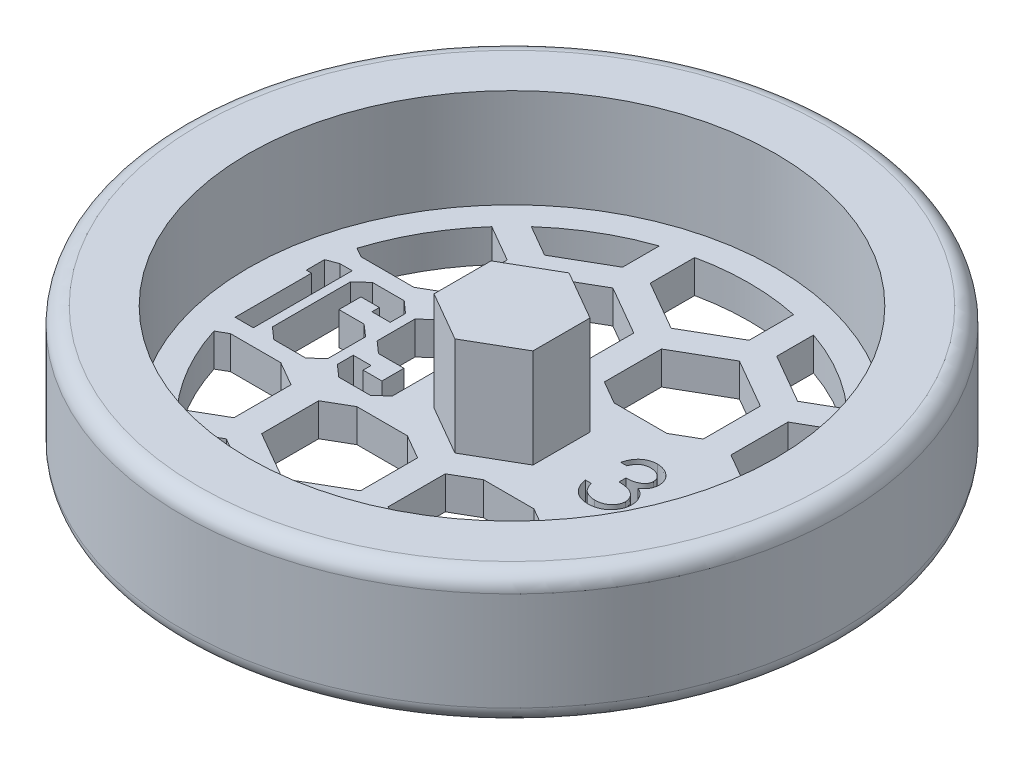
SolidWorks part; units mm, degrees
ref_plane "Front Plane" through (0, 0, 0) normal (0, 0, 1) x (1, 0, 0)
ref_plane "Top Plane" through (0, 0, 0) normal (0, 1, 0) x (1, 0, 0)
ref_plane "Right Plane" through (0, 0, 0) normal (1, 0, 0) x (0, 0, -1)
sketch "Sketch1" plane through (0, 0, 0) normal (0, 0, 1) x (1, 0, 0)
  line L0 (0, 0) -> (30.1625, 0)
  line L1 (31.75, 1.5875) -> (31.75, 11.1125)
  line L2 (30.1625, 12.7) -> (25.4, 12.7)
  line L3 (25.4, 12.7) -> (25.4, 3.175)
  line L4 (25.4, 3.175) -> (0, 3.175)
  line L5 (0, 3.175) -> (0, 0)
  arc A0 (30.1625, 0) -> (31.75, 1.5875) centre (30.1625, 1.5875) ccw
  arc A1 (31.75, 11.1125) -> (30.1625, 12.7) centre (30.1625, 11.1125) ccw
  dimension "D5" = 1.5875
  dimension "D1" = 6.35
  dimension "D2" = 3.175
  dimension "D3" = 25.4
  dimension "D4" = 9.525
revolve "Revolve1" add sketch "Sketch1" angle 360 about L5
sketch "Sketch2" plane through (0, 3.175, 0) normal (0, 1, 0) x (1, 0, 0)
  line L1 (0, -5.4993) -> (4.7625, -2.7496)
  line L2 (4.7625, -2.7496) -> (4.7625, 2.7496)
  line L3 (4.7625, 2.7496) -> (0, 5.4993)
  line L4 (0, 5.4993) -> (-4.7625, 2.7496)
  line L5 (-4.7625, 2.7496) -> (-4.7625, -2.7496)
  line L6 (-4.7625, -2.7496) -> (0, -5.4993)
  circle A0 centre (0, 0) radius 4.7625 construction
  dimension "D1" = 9.525
extrude "Boss-Extrude1" add sketch "Sketch2" along normal blind 9.525
sketch "Sketch3" plane through (0, 3.175, 0) normal (0, 1, 0) x (1, 0, 0)
  line L0 (-4.7625, 0) -> (-25.4, 0) construction
  line L1 (-4.7625, 2.7496) -> (-4.7625, -2.7496) construction
  line L2 (-25.4, -4.7625) -> (-4.7625, -4.7625) construction
  line L3 (4.7625, 0) -> (25.4, 0) construction
  line L4 (4.7625, -2.7496) -> (4.7625, 2.7496) construction
  line L5 (4.7625, -3.175) -> (25.4, -3.175) construction
  circle A0 centre (0, 0) radius 25.4 construction
  circle A1 centre (0, 0) radius 25.4 construction
  text T0 "169" font "Jersey M54" height 9.525
  text T1 "3/8" font "Century Gothic" height 6.35
  dimension "D1" = 4.7625
  dimension "D2" = 3.175
extrude "Cut-Extrude1" cut sketch "Sketch3" against normal through all both and the other way through all
sketch "Sketch4" plane through (0, 3.175, 0) normal (0, 1, 0) x (1, 0, 0)
  line L0 (0, -6.35) -> (0, 6.35)
  line L1 (-21.9604, 6.35) -> (21.9604, 6.35)
  line L2 (-21.9604, -6.35) -> (21.9604, -6.35)
  line L3 (7.4295, -2.7496) -> (12.192, -5.4993)
  line L4 (0, -5.4993) -> (4.7625, -2.7496)
  line L5 (4.7625, -2.7496) -> (4.7625, 2.7496)
  line L6 (4.7625, 2.7496) -> (0, 5.4993)
  line L7 (0, 5.4993) -> (-4.7625, 2.7496)
  line L8 (-4.7625, 2.7496) -> (-4.7625, -2.7496)
  line L9 (-4.7625, -2.7496) -> (0, -5.4993)
  line L10 (6.0325, -4.9493) -> (1.27, -7.699)
  line L11 (1.27, -7.699) -> (1.27, -13.1982)
  line L12 (1.27, -13.1982) -> (6.0325, -15.9479)
  line L13 (6.0325, -15.9479) -> (10.795, -13.1982)
  line L14 (10.795, -13.1982) -> (10.795, -7.699)
  line L15 (10.795, -7.699) -> (6.0325, -4.9493)
  line L16 (7.4295, 2.7496) -> (7.4295, -2.7496)
  line L17 (12.192, 5.4993) -> (7.4295, 2.7496)
  line L18 (16.9545, 2.7496) -> (12.192, 5.4993)
  line L19 (16.9545, -2.7496) -> (16.9545, 2.7496)
  line L20 (12.192, -5.4993) -> (16.9545, -2.7496)
  line L21 (18.2245, -4.9493) -> (13.462, -7.699)
  line L22 (13.462, -7.699) -> (13.462, -13.1982)
  line L23 (13.462, -13.1982) -> (18.2245, -15.9479)
  line L24 (18.2245, -15.9479) -> (22.987, -13.1982)
  line L25 (22.987, -13.1982) -> (22.987, -7.699)
  line L26 (22.987, -7.699) -> (18.2245, -4.9493)
  line L27 (19.6215, -2.7496) -> (24.384, -5.4993)
  line L28 (19.6215, 2.7496) -> (19.6215, -2.7496)
  line L29 (24.384, 5.4993) -> (19.6215, 2.7496)
  line L30 (29.1465, 2.7496) -> (24.384, 5.4993)
  line L31 (29.1465, -2.7496) -> (29.1465, 2.7496)
  line L32 (24.384, -5.4993) -> (29.1465, -2.7496)
  line L33 (30.4165, -4.9493) -> (25.654, -7.699)
  line L34 (25.654, -7.699) -> (25.654, -13.1982)
  line L35 (25.654, -13.1982) -> (30.4165, -15.9479)
  line L36 (30.4165, -15.9479) -> (35.179, -13.1982)
  line L37 (35.179, -13.1982) -> (35.179, -7.699)
  line L38 (35.179, -7.699) -> (30.4165, -4.9493)
  line L39 (-16.9545, -2.7496) -> (-12.192, -5.4993)
  line L40 (-16.9545, 2.7496) -> (-16.9545, -2.7496)
  line L41 (-12.192, 5.4993) -> (-16.9545, 2.7496)
  line L42 (-7.4295, 2.7496) -> (-12.192, 5.4993)
  line L43 (-7.4295, -2.7496) -> (-7.4295, 2.7496)
  line L44 (-12.192, -5.4993) -> (-7.4295, -2.7496)
  line L45 (-6.1595, -4.9493) -> (-10.922, -7.699)
  line L46 (-10.922, -7.699) -> (-10.922, -13.1982)
  line L47 (-10.922, -13.1982) -> (-6.1595, -15.9479)
  line L48 (-6.1595, -15.9479) -> (-1.397, -13.1982)
  line L49 (-1.397, -13.1982) -> (-1.397, -7.699)
  line L50 (-1.397, -7.699) -> (-6.1595, -4.9493)
  line L51 (-29.1465, -2.7496) -> (-24.384, -5.4993)
  line L52 (-29.1465, 2.7496) -> (-29.1465, -2.7496)
  line L53 (-24.384, 5.4993) -> (-29.1465, 2.7496)
  line L54 (-19.6215, 2.7496) -> (-24.384, 5.4993)
  line L55 (-19.6215, -2.7496) -> (-19.6215, 2.7496)
  line L56 (-24.384, -5.4993) -> (-19.6215, -2.7496)
  line L57 (-18.3515, -4.9493) -> (-23.114, -7.699)
  line L58 (-23.114, -7.699) -> (-23.114, -13.1982)
  line L59 (-23.114, -13.1982) -> (-18.3515, -15.9479)
  line L60 (-18.3515, -15.9479) -> (-13.589, -13.1982)
  line L61 (-13.589, -13.1982) -> (-13.589, -7.699)
  line L62 (-13.589, -7.699) -> (-18.3515, -4.9493)
  line L63 (-29.1465, 18.0784) -> (-24.384, 15.3287)
  line L64 (-24.384, 15.3287) -> (-19.6215, 18.0784)
  line L65 (-19.6215, 18.0784) -> (-19.6215, 23.5776)
  line L66 (-19.6215, 23.5776) -> (-24.384, 26.3273)
  line L67 (-24.384, 26.3273) -> (-29.1465, 23.5776)
  line L68 (-29.1465, 23.5776) -> (-29.1465, 18.0784)
  line L69 (-18.3515, 15.8787) -> (-23.114, 13.129)
  line L70 (-23.114, 13.129) -> (-23.114, 7.6298)
  line L71 (-23.114, 7.6298) -> (-18.3515, 4.8801)
  line L72 (-18.3515, 4.8801) -> (-13.589, 7.6298)
  line L73 (-13.589, 7.6298) -> (-13.589, 13.129)
  line L74 (-13.589, 13.129) -> (-18.3515, 15.8787)
  line L75 (-16.9545, 18.0784) -> (-12.192, 15.3287)
  line L76 (-12.192, 15.3287) -> (-7.4295, 18.0784)
  line L77 (-7.4295, 18.0784) -> (-7.4295, 23.5776)
  line L78 (-7.4295, 23.5776) -> (-12.192, 26.3273)
  line L79 (-12.192, 26.3273) -> (-16.9545, 23.5776)
  line L80 (-16.9545, 23.5776) -> (-16.9545, 18.0784)
  line L81 (-6.1595, 15.8787) -> (-10.922, 13.129)
  line L82 (-10.922, 13.129) -> (-10.922, 7.6298)
  line L83 (-10.922, 7.6298) -> (-6.1595, 4.8801)
  line L84 (-6.1595, 4.8801) -> (-1.397, 7.6298)
  line L85 (-1.397, 7.6298) -> (-1.397, 13.129)
  line L86 (-1.397, 13.129) -> (-6.1595, 15.8787)
  line L87 (6.0325, 15.8787) -> (1.27, 13.129)
  line L88 (1.27, 13.129) -> (1.27, 7.6298)
  line L89 (1.27, 7.6298) -> (6.0325, 4.8801)
  line L90 (6.0325, 4.8801) -> (10.795, 7.6298)
  line L91 (10.795, 7.6298) -> (10.795, 13.129)
  line L92 (10.795, 13.129) -> (6.0325, 15.8787)
  line L93 (-4.7625, 18.0784) -> (0, 15.3287)
  line L94 (-4.7625, 23.5776) -> (-4.7625, 18.0784)
  line L95 (0, 26.3273) -> (-4.7625, 23.5776)
  line L96 (4.7625, 23.5776) -> (0, 26.3273)
  line L97 (4.7625, 18.0784) -> (4.7625, 23.5776)
  line L98 (0, 15.3287) -> (4.7625, 18.0784)
  line L99 (7.4295, 18.0784) -> (12.192, 15.3287)
  line L100 (12.192, 15.3287) -> (16.9545, 18.0784)
  line L101 (16.9545, 18.0784) -> (16.9545, 23.5776)
  line L102 (16.9545, 23.5776) -> (12.192, 26.3273)
  line L103 (12.192, 26.3273) -> (7.4295, 23.5776)
  line L104 (7.4295, 23.5776) -> (7.4295, 18.0784)
  line L105 (19.6215, 18.0784) -> (24.384, 15.3287)
  line L106 (24.384, 15.3287) -> (29.1465, 18.0784)
  line L107 (29.1465, 18.0784) -> (29.1465, 23.5776)
  line L108 (29.1465, 23.5776) -> (24.384, 26.3273)
  line L109 (24.384, 26.3273) -> (19.6215, 23.5776)
  line L110 (19.6215, 23.5776) -> (19.6215, 18.0784)
  line L111 (18.2245, 15.8787) -> (13.462, 13.129)
  line L112 (13.462, 13.129) -> (13.462, 7.6298)
  line L113 (13.462, 7.6298) -> (18.2245, 4.8801)
  line L114 (18.2245, 4.8801) -> (22.987, 7.6298)
  line L115 (22.987, 7.6298) -> (22.987, 13.129)
  line L116 (22.987, 13.129) -> (18.2245, 15.8787)
  line L117 (30.4165, 15.8787) -> (25.654, 13.129)
  line L118 (25.654, 13.129) -> (25.654, 7.6298)
  line L119 (25.654, 7.6298) -> (30.4165, 4.8801)
  line L120 (30.4165, 4.8801) -> (35.179, 7.6298)
  line L121 (35.179, 7.6298) -> (35.179, 13.129)
  line L122 (35.179, 13.129) -> (30.4165, 15.8787)
  line L123 (-29.1465, -23.5776) -> (-24.384, -26.3273)
  line L124 (-24.384, -26.3273) -> (-19.6215, -23.5776)
  line L125 (-19.6215, -23.5776) -> (-19.6215, -18.0784)
  line L126 (-19.6215, -18.0784) -> (-24.384, -15.3287)
  line L127 (-24.384, -15.3287) -> (-29.1465, -18.0784)
  line L128 (-29.1465, -18.0784) -> (-29.1465, -23.5776)
  line L129 (-18.3515, -25.7773) -> (-23.114, -28.527)
  line L130 (-23.114, -28.527) -> (-23.114, -34.0262)
  line L131 (-23.114, -34.0262) -> (-18.3515, -36.7759)
  line L132 (-18.3515, -36.7759) -> (-13.589, -34.0262)
  line L133 (-13.589, -34.0262) -> (-13.589, -28.527)
  line L134 (-13.589, -28.527) -> (-18.3515, -25.7773)
  line L135 (-16.9545, -23.5776) -> (-12.192, -26.3273)
  line L136 (-12.192, -26.3273) -> (-7.4295, -23.5776)
  line L137 (-7.4295, -23.5776) -> (-7.4295, -18.0784)
  line L138 (-7.4295, -18.0784) -> (-12.192, -15.3287)
  line L139 (-12.192, -15.3287) -> (-16.9545, -18.0784)
  line L140 (-16.9545, -18.0784) -> (-16.9545, -23.5776)
  line L141 (-6.1595, -25.7773) -> (-10.922, -28.527)
  line L142 (-10.922, -28.527) -> (-10.922, -34.0262)
  line L143 (-10.922, -34.0262) -> (-6.1595, -36.7759)
  line L144 (-6.1595, -36.7759) -> (-1.397, -34.0262)
  line L145 (-1.397, -34.0262) -> (-1.397, -28.527)
  line L146 (-1.397, -28.527) -> (-6.1595, -25.7773)
  line L147 (6.0325, -25.7773) -> (1.27, -28.527)
  line L148 (1.27, -28.527) -> (1.27, -34.0262)
  line L149 (1.27, -34.0262) -> (6.0325, -36.7759)
  line L150 (6.0325, -36.7759) -> (10.795, -34.0262)
  line L151 (10.795, -34.0262) -> (10.795, -28.527)
  line L152 (10.795, -28.527) -> (6.0325, -25.7773)
  line L153 (-4.7625, -23.5776) -> (0, -26.3273)
  line L154 (-4.7625, -18.0784) -> (-4.7625, -23.5776)
  line L155 (0, -15.3287) -> (-4.7625, -18.0784)
  line L156 (4.7625, -18.0784) -> (0, -15.3287)
  line L157 (4.7625, -23.5776) -> (4.7625, -18.0784)
  line L158 (0, -26.3273) -> (4.7625, -23.5776)
  line L159 (7.4295, -23.5776) -> (12.192, -26.3273)
  line L160 (12.192, -26.3273) -> (16.9545, -23.5776)
  line L161 (16.9545, -23.5776) -> (16.9545, -18.0784)
  line L162 (16.9545, -18.0784) -> (12.192, -15.3287)
  line L163 (12.192, -15.3287) -> (7.4295, -18.0784)
  line L164 (7.4295, -18.0784) -> (7.4295, -23.5776)
  line L165 (19.6215, -23.5776) -> (24.384, -26.3273)
  line L166 (24.384, -26.3273) -> (29.1465, -23.5776)
  line L167 (29.1465, -23.5776) -> (29.1465, -18.0784)
  line L168 (29.1465, -18.0784) -> (24.384, -15.3287)
  line L169 (24.384, -15.3287) -> (19.6215, -18.0784)
  line L170 (19.6215, -18.0784) -> (19.6215, -23.5776)
  line L171 (18.2245, -25.7773) -> (13.462, -28.527)
  line L172 (13.462, -28.527) -> (13.462, -34.0262)
  line L173 (13.462, -34.0262) -> (18.2245, -36.7759)
  line L174 (18.2245, -36.7759) -> (22.987, -34.0262)
  line L175 (22.987, -34.0262) -> (22.987, -28.527)
  line L176 (22.987, -28.527) -> (18.2245, -25.7773)
  line L177 (30.4165, -25.7773) -> (25.654, -28.527)
  line L178 (25.654, -28.527) -> (25.654, -34.0262)
  line L179 (25.654, -34.0262) -> (30.4165, -36.7759)
  line L180 (30.4165, -36.7759) -> (35.179, -34.0262)
  line L181 (35.179, -34.0262) -> (35.179, -28.527)
  line L182 (35.179, -28.527) -> (30.4165, -25.7773)
  circle A0 centre (0, 0) radius 22.86
  circle A1 centre (0, 0) radius 4.7625 construction
  circle A2 centre (6.0325, -10.4486) radius 4.7625 construction
  point P6 (0, 0)
  point P9 (0, 6.35)
  point P12 (0, -6.35)
  dimension "D1" = 45.72
  dimension "D2" = 12.7
  dimension "D3" = 9.525
  dimension "D4" = 9.525
  dimension "D5" = 2.54
  dimension "D6" = 1.27
  dimension "D9" = 2.1997
  dimension "D7" = 3
  dimension "D8" = 3
  dimension "D10" = 2
  dimension "D11" = 2
extrude "Cut-Extrude3" cut sketch "Sketch4" against normal through all both and the other way through all contours L74 A0 L71 L1 L72 L73 | L77 A0 L75 L76 | L85 L86 L81 L82 L83 L1 L84 | L97 A0 L94 L93 L98 | L91 L92 L87 L88 L89 L1 L90 | L100 A0 L104 L99 | L114 A0 L111 L112 L113 L1 | L23 A0 L26 L2 L21 L22 | L164 A0 L162 L163 | L14 L15 L2 L10 L11 L12 L13 | L154 A0 L157 L156 L155 | L49 L50 L2 L45 L46 L47 L48 | L139 A0 L137 L138 | L57 A0 L60 L61 L62 L2
